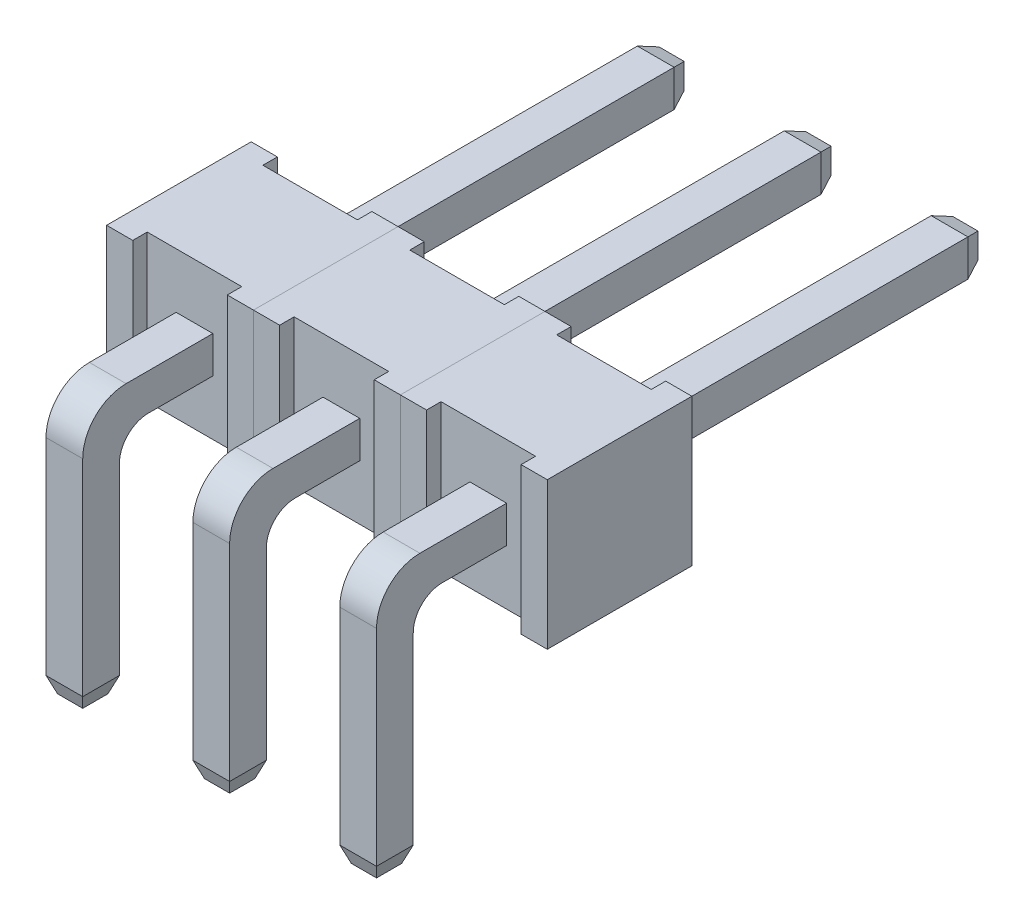
SolidWorks part; units mm, degrees
ref_plane "Front Plane" through (0, 0, 0) normal (0, 0, 1) x (1, 0, 0)
ref_plane "Top Plane" through (0, 0, 0) normal (0, 1, 0) x (1, 0, 0)
ref_plane "Right Plane" through (0, 0, 0) normal (1, 0, 0) x (0, 0, -1)
sketch "Sketch1" plane through (0, 0, 0) normal (0, 0, 1) x (1, 0, 0)
  line L0 (2.54, 5.54) -> (2.54, 3) construction
  line L1 (0, 5.54) -> (13.2523, 5.54)
  line L2 (0, 5.54) -> (0, 3)
  line L3 (0, 3) -> (13.2523, 3)
  line L4 (13.2523, 5.54) -> (13.2523, 3)
  line L5 (1.5875, 4.5875) -> (0.9525, 4.5875)
  line L6 (1.5875, 4.5875) -> (1.5875, 0)
  line L7 (1.5875, 0) -> (0.9525, 0)
  line L8 (0.9525, 4.5875) -> (0.9525, 0)
  line L9 (3.4925, 4.5875) -> (4.1275, 4.5875)
  line L10 (3.4925, 4.5875) -> (3.4925, 0)
  line L11 (3.4925, 0) -> (4.1275, 0)
  line L12 (4.1275, 4.5875) -> (4.1275, 0)
  line L14 (0.9525, 3.9525) -> (1.5875, 3.9525)
  line L15 (0.9525, 3.9525) -> (0.9525, 4.5875)
  line L16 (0.9525, 4.5875) -> (1.5875, 4.5875)
  line L17 (1.5875, 3.9525) -> (1.5875, 4.5875)
  line L18 (0.9525, 3.9525) -> (1.5875, 4.5875) construction
  line L19 (0.9525, 4.5875) -> (1.5875, 3.9525) construction
  point P12 (1.27, 4.5875)
  point P16 (1.27, 4.27)
  point P22 (0, 4.27)
  dimension "D1" = 0.635
  dimension "D2" = 2.54
  dimension "D3" = 2.54
  dimension "D4" = 1.27
  dimension "D5" = 2.54
  dimension "D6" = 3
sketch "Sketch2" plane through (0, 0, 0) normal (0, 0, 1) x (1, 0, 0)
  line L1 (0.9525, 0) -> (1.5875, 0)
  line L2 (0.9525, 0) -> (0.9525, 4.5875)
  line L3 (0.9525, 4.5875) -> (1.5875, 4.5875)
  line L4 (1.5875, 0) -> (1.5875, 4.5875)
extrude "Boss-Extrude1" add sketch "Sketch2" against normal blind 0.635
sketch "Sketch3" plane through (0, 0, -0.635) normal (0, 0, -1) x (-1, 0, 0)
  line L0 (-1.5875, 0) -> (-1.5875, 4.5875) construction
  line L1 (-0.9525, 4.5875) -> (-1.5875, 4.5875)
  line L2 (-0.9525, 4.5875) -> (-0.9525, 3.9525)
  line L3 (-0.9525, 3.9525) -> (-1.5875, 3.9525)
  line L4 (-1.5875, 4.5875) -> (-1.5875, 3.9525)
extrude "Boss-Extrude2" add sketch "Sketch3" along normal offset from surface (9.865 mm away) 10.5 up to face at (1.27, 2.2938, 0)
fillet "Fillet1" radius 0.5 1 edges at (1.27, 3.9525, -0.635)
fillet "Fillet2" radius 0.75 1 edges at (1.27, 4.5875, 0)
ref_plane "Plane1" through (0, 0, -2) normal (0, 0, -1) x (-1, 0, 0)
sketch "Sketch4" plane through (0, 0, -2) normal (0, 0, -1) x (-1, 0, 0)
  line L0 (0, 3) -> (-13.2523, 3) construction
  line L1 (0, 5.54) -> (-0.4525, 5.54)
  line L2 (0, 5.54) -> (0, 3)
  line L3 (0, 3) -> (-0.4525, 3)
  line L4 (-0.4525, 5.54) -> (-0.4525, 3)
  line L5 (-0.9525, 4.5875) -> (-0.9525, 0) construction
  line L6 (-2.54, 5.54) -> (-2.0875, 5.54)
  line L7 (-2.54, 5.54) -> (-2.54, 3)
  line L8 (-2.54, 3) -> (-2.0875, 3)
  line L9 (-2.0875, 5.54) -> (-2.0875, 3)
  point P14 (0, 5.54)
  dimension "D1" = 0.5
extrude "Boss-Extrude3" add sketch "Sketch4" along normal blind 0.25 separate body
sketch "Sketch5" plane through (0, 0, -2.25) normal (0, 0, -1) x (-1, 0, 0)
  line L1 (-2.54, 5.54) -> (0, 5.54)
  line L2 (-2.54, 5.54) -> (-2.54, 3)
  line L3 (-2.54, 3) -> (0, 3)
  line L4 (0, 5.54) -> (0, 3)
extrude "Boss-Extrude4" add sketch "Sketch5" along normal blind 2
sketch "Sketch6" plane through (0, 0, -4.25) normal (0, 0, -1) x (-1, 0, 0)
  line L1 (-0.4525, 5.54) -> (0, 5.54)
  line L2 (-0.4525, 5.54) -> (-0.4525, 3)
  line L3 (-0.4525, 3) -> (0, 3)
  line L4 (0, 5.54) -> (0, 3)
  line L5 (-2.0875, 5.54) -> (-2.54, 5.54)
  line L6 (-2.0875, 5.54) -> (-2.0875, 3)
  line L7 (-2.0875, 3) -> (-2.54, 3)
  line L8 (-2.54, 5.54) -> (-2.54, 3)
extrude "Boss-Extrude5" add sketch "Sketch6" along normal blind 0.25
chamfer "Chamfer1" distance 0.1 angle 70 4 edges at (1.27, 3.9525, -10.5) (0.9525, 4.27, -10.5) (1.27, 4.5875, -10.5) (1.5875, 4.27, -10.5)
chamfer "Chamfer2" distance 0.1 angle 70 4 edges at (1.27, 0, 0) (1.5875, 0, -0.3175) (0.9525, 0, -0.3175) (1.27, 0, -0.635)
pattern_linear "Num pins" count 3 spacing 2.54 along (1, 0, 0) of bodies 106
